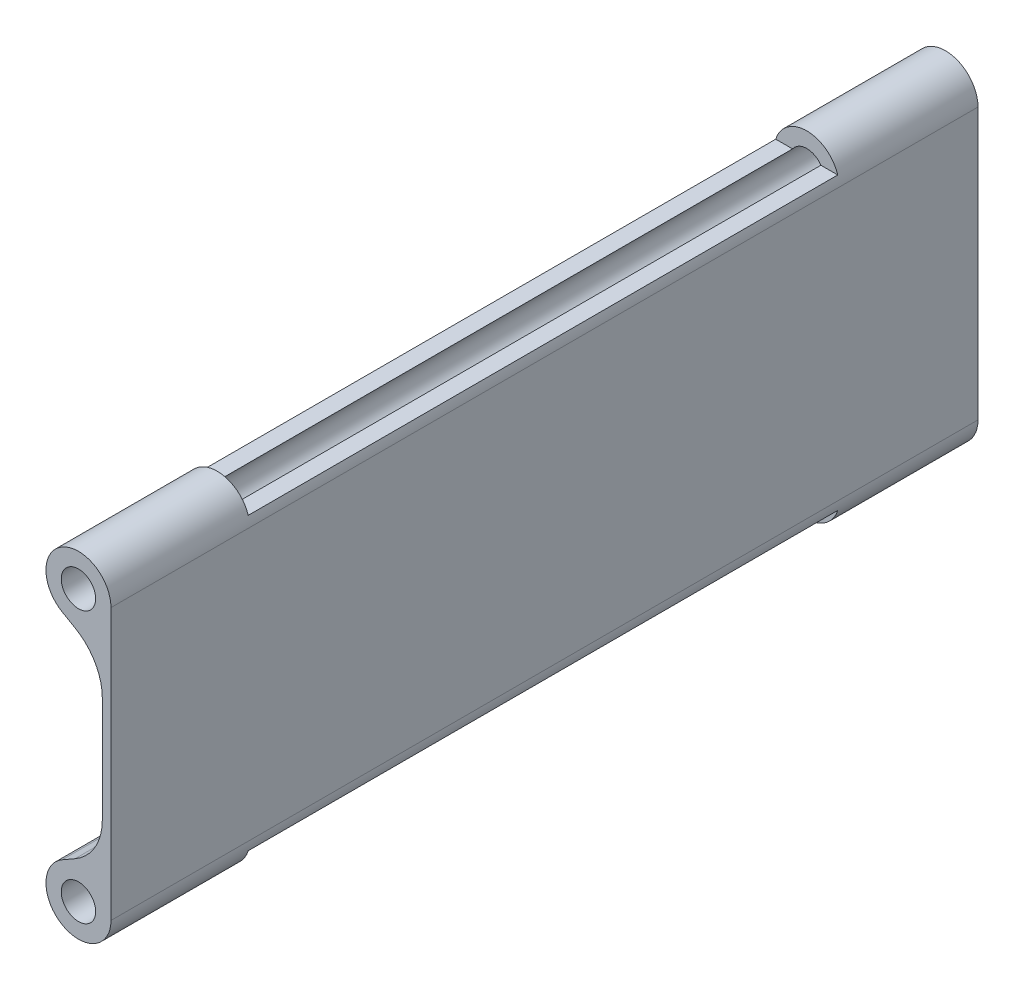
SolidWorks part; units mm, degrees
material "ABS"
ref_plane "Alzado" through (0, 0, 0) normal (0, 0, 1) x (1, 0, 0)
ref_plane "Planta" through (0, 0, 0) normal (0, 1, 0) x (1, 0, 0)
ref_plane "Vista lateral" through (0, 0, 0) normal (1, 0, 0) x (0, 0, -1)
sketch "Croquis1" plane through (0, 0, 0) normal (0, 0, 1) x (1, 0, 0)
  line L5 (-13.465, 0) -> (13.8234, 0) construction
  line L8 (-1.6, 15.5562) -> (-8.9869, 19.7963)
  line L9 (-1.6, 15.5562) -> (-1.6, -15.5562)
  line L10 (0, 25) -> (0, -25)
  line L11 (-1.6, -15.5562) -> (-8.9869, -19.7963)
  circle A0 centre (-6, 25) radius 3.175
  arc A5 (0, 25) -> (-8.9869, 19.7963) centre (-6, 25) ccw
  arc A6 (0, -25) -> (-8.9869, -19.7963) centre (-6, -25) cw
  circle A7 centre (-6, -25) radius 3.175
  point P7 (0, 0)
  point P15 (0, 0)
  point P16 (-1.6, 0)
  point P17 (-1.6, 0)
  dimension "D1" = 6.35
  dimension "D2" = 50
  dimension "D3" = 1.6
  dimension "D4" = 6
extrude "Saliente-Extruir1" add sketch "Croquis1" against normal blind 160
fillet "Redondeo1" radius 10 2 edges at (-1.6, -15.5562, -80) (-1.6, 15.5562, -80)
sketch "Croquis3" plane through (0, 0, 0) normal (1, 0, 0) x (0, 0, -1)
  line L0 (0, 0) -> (160, 0) construction
  line L1 (25.6041, 44.9478) -> (134.3959, 44.9478)
  line L2 (25.6041, 44.9478) -> (25.6041, 26.8024)
  line L3 (25.6041, 26.8024) -> (134.3959, 26.8024)
  line L4 (134.3959, 44.9478) -> (134.3959, 26.8024)
  line L5 (134.3959, -44.9478) -> (134.3959, -26.8024)
  line L6 (25.6041, -26.8024) -> (134.3959, -26.8024)
  line L7 (25.6041, -44.9478) -> (25.6041, -26.8024)
  line L8 (25.6041, -44.9478) -> (134.3959, -44.9478)
  line L9 (160, 9.7659) -> (160, -9.7659) construction
  point P16 (80, 0)
  point P17 (80, -26.8024)
extrude "Cortar-Extruir2" cut sketch "Croquis3" against normal through all
